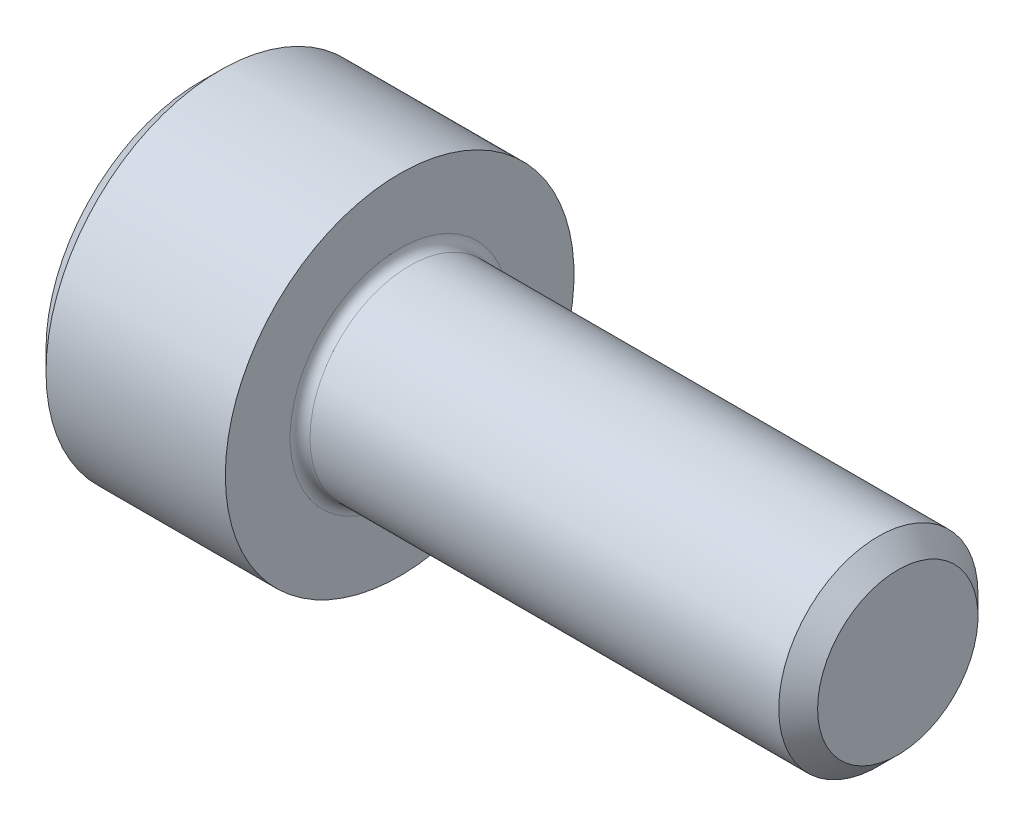
SolidWorks part; units mm, degrees
ref_plane "Plane1" through (0, 0, 0) normal (0, 0, 1) x (1, 0, 0)
ref_plane "Plane2" through (0, 0, 0) normal (0, 1, 0) x (1, 0, 0)
ref_plane "Plane3" through (0, 0, 0) normal (1, 0, 0) x (0, 0, -1)
revolve "Base-Revolve" add sketch "BodySke"
sketch "BodySke" plane through (0, 0, 0) normal (0, 0, 1) x (1, 0, 0)
  line L0 (0, 0) -> (0, 3.1)
  line L1 (0.4, 3.5) -> (4, 3.5)
  line L2 (4, 3.5) -> (4, 2)
  line L3 (4, 2) -> (13.61, 2)
  line L4 (14, 1.61) -> (14, 0)
  line L5 (14, 0) -> (0, 0)
  line L6 (-31.75, 0) -> (127, 0) construction
  line L7 (0, 3.1) -> (0.4, 3.5)
  line L8 (14, 1.61) -> (13.61, 2)
  line L9 (0, -3.1) -> (0.4, -3.5) construction
  line L10 (14, -1.61) -> (13.61, -2) construction
  line L11 (4.7, 9.525) -> (4.7, 3.175) construction
  line L12 (4, 9.525) -> (4, 3.175) construction
  line L13 (-36, 9.525) -> (-36, 3.175) construction
  dimension "Diameter" = 4
  dimension "Head_ht" = 4
  dimension "Length" = 10
  dimension "Body_ch_ang" = 45
  dimension "Head_dia" = 7
  dimension "Head_ch_ang" = 45
  dimension "Minor_dia" = 3.22
  dimension "Advance" = 0.7
  dimension "Thread_nom" = 10
  dimension "Thread_length" = 50
  dimension "Head_ch_ht" = 0.4
cosmetic thread "ThreadCosmetic" [suppressed]
fillet "Fillet1" radius 0.2 1 edges at (4, 0, 2)
sketch "Sketch2" plane through (0, 0, 0) normal (0, 0, 1) x (1, 0, 0)
  line L0 (0, 1.5355) -> (2, 1.5355)
  line L1 (2, 1.5355) -> (2.8865, 0)
  line L2 (-31.75, 0) -> (127, 0) construction
  line L3 (2.8865, 0) -> (0, 0)
  line L4 (0, 0) -> (0, 1.5355)
  line L5 (0, 3.1) -> (0, -3.1) construction
  line L6 (0, 0) -> (47.625, 0) construction
  line L7 (4, -3.5) -> (4, 3.5) construction
  dimension "D1" = 1.5355
  dimension "D2" = 60
  dimension "Wall_thickness" = 2
revolve "Hex-PreBroach" cut sketch "Sketch2" angle 360 about L6
sketch "Sketch3" plane through (0, 0, 0) normal (-1, 0, 0) x (0, 0.5, 0.866)
  line L0 (0.8865, 1.5355) -> (-0.8865, 1.5355)
  line L1 (-0.8865, 1.5355) -> (-1.773, 0)
  line L2 (0.8865, 1.5355) -> (1.773, 0)
  line L3 (0.8865, -1.5355) -> (1.773, 0)
  line L4 (0.8865, -1.5355) -> (-0.8865, -1.5355)
  line L5 (-0.8865, -1.5355) -> (-1.773, 0)
  dimension "D1" = 1.5355
  dimension "D2" = 1.5355
  dimension "Hex_size" = 3.071
extrude "Hex" cut sketch "Sketch3" against normal blind 2
sketch "Sketch4" plane through (0, 0, 0) normal (-1, 0, 0) x (0, 0, 1)
  line L0 (0, 0) -> (1.7399, 0)
  line L1 (0, 0) -> (6.1484, 3.5498) construction
  line L2 (0, 0) -> (0.8699, 1.5068)
  line L3 (1.4457, 0.3947) -> (1.6607, 0.5189)
  line L4 (1.0647, 1.0546) -> (1.2797, 1.1788)
  arc A0 (1.4457, 0.3947) -> (1.0647, 1.0546) centre (0, 0) ccw
  arc A1 (1.7399, 0) -> (1.6607, 0.5189) centre (0, 0) ccw
  arc A2 (0.8699, 1.5068) -> (1.2797, 1.1788) centre (0, 0) cw
  dimension "D1" = 30
  dimension "Spline_n_dim" = 2.9972
  dimension "Spline_m_dim" = 3.4798
  dimension "D2" = 60
  dimension "D3" = 0.381
  dimension "Spline_p_dim" = 0.762
extrude "Spline" [suppressed] cut sketch "Sketch4" against normal blind 2
pattern_circular "CirPattern1" [suppressed] count 6 every 60
sketch "Sketch5" plane through (0, 0, 0) normal (0, 0, 1) x (1, 0, 0)
  line L0 (-31.75, 0) -> (127, 0) construction
  line L2 (0, 3.1) -> (0, -3.1) construction
  circle A0 centre (1.6, 0) radius 0.675
  dimension "Drilled_hole_dia" = 1.35
  dimension "Drilled_hole_loc" = 1.6
extrude "Hole" [suppressed] cut sketch "Sketch5" against normal through all and the other way through all
pattern_circular "Drilled-4" [suppressed] count 2 every 60
pattern_circular "Drilled-6" [suppressed] count 3 every 60
sketch "ThdSchSke" plane through (0, 0, 0) normal (0, 0, 1) x (1, 0, 0)
  line L0 (4.7, -1.61) -> (4.4269, -2)
  line L1 (4.7, -1.61) -> (4.9731, -2)
  line L2 (4.9731, -2) -> (4.9731, -2.5)
  line L3 (-3.175, 0) -> (5.1513, 0) construction
  line L5 (4.9731, -2.5) -> (4.4269, -2.5)
  line L6 (4.4269, -2.5) -> (4.4269, -2)
  line L7 (0, 3.1) -> (0, -3.1) construction
  dimension "Thread_minor" = 3.22
  dimension "Diameter" = 4
  dimension "Start" = 4.7
  dimension "SideAngle" = 55
  dimension "VeeAngle" = 70
  dimension "Overcut" = 5
revolve "ThreadSchematic" [suppressed] cut sketch "ThdSchSke" angle 360 about L3
pattern_linear "ThdSchPat" [suppressed]
equation "\"D2@Sketch3\" = \"Hex_size@Sketch3\" / 2"
equation "\"D1@Sketch3\" = \"Hex_size@Sketch3\" / 2"
equation "\"D1@Sketch2\" = \"Hex_size@Sketch3\" / 2"
equation "\"D3@Sketch4\" = \"Spline_p_dim@Sketch4\" / 2"
equation "\"Thread_minor@ThreadCosmetic\"  =  \"Minor_dia@BodySke\""
equation "\"D2@CirPattern1\" = 360 / \"Num_teeth@CirPattern1\""
equation "\"Wall_thickness@Sketch2\" = \"Head_ht@BodySke\" - \"Key_eng@Hex\""
equation "\"Thread_length@ThreadCosmetic\" = ((sgn( (\"Length@BodySke\" - \"Advance@BodySke\" ) - \"Thread_nom@BodySke\" )-1)*( (\"Length@BodySke\" - \"Advance@BodySke\" ) - \"Thread_nom@BodySke\" ))/-2+ \"Thread_nom@BodySke\""
equation "\"Thread_minor@ThdSchSke\" = \"Minor_dia@BodySke\""
equation "\"Diameter@ThdSchSke\" = \"Diameter@BodySke\""
equation "\"Overcut@ThdSchSke\" = \"Diameter@BodySke\" * 1.25"
equation "\"Start@ThdSchSke\" = \"Head_ht@BodySke\" + \"Length@BodySke\" - \"Thread_length@ThreadCosmetic\"  '---Non-countersunk---"
equation "\"Num_threads@ThdSchPat\" = int( \"Thread_length@ThreadCosmetic\" / \"Advance@BodySke\" + 0.999 )  + 1"
equation "\"Advance@ThdSchPat\" = \"Thread_length@ThreadCosmetic\" /  (\"Num_threads@ThdSchPat\" - 1) 'relax it"
equation "\"Num_threads@ThdSchPat\" = \"Num_threads@ThdSchPat\" - sgn( \"Num_threads@ThdSchPat\" - 1) '---chamfered tips only---"
